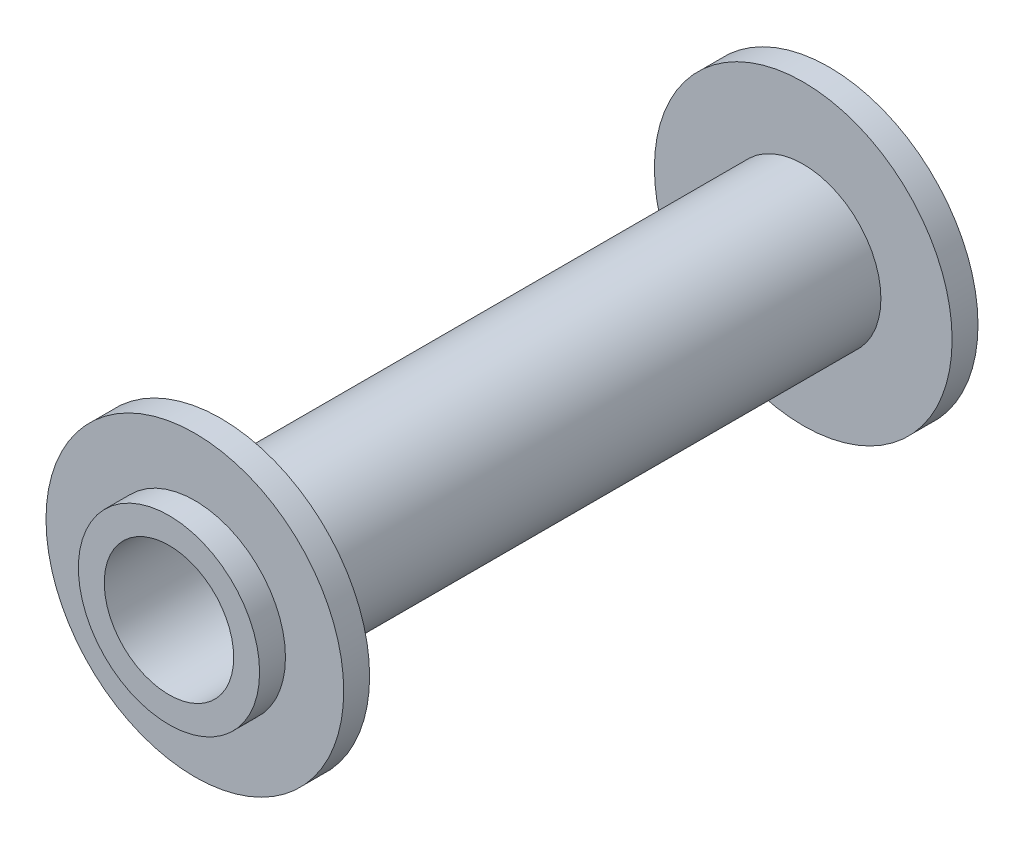
SolidWorks part; units mm, degrees
material "1060 Alloy"
ref_plane "Front Plane" through (0, 0, 0) normal (0, 0, 1) x (1, 0, 0)
ref_plane "Top Plane" through (0, 0, 0) normal (0, 1, 0) x (1, 0, 0)
ref_plane "Right Plane" through (0, 0, 0) normal (1, 0, 0) x (0, 0, -1)
sketch "Sketch2" plane through (0, 0, 0) normal (1, 0, 0) x (0, 0, -1)
  line L0 (0, 0) -> (56.7425, 0) construction
  line L1 (0, 5) -> (0, 7)
  line L2 (4, 6) -> (4, 11.5)
  line L3 (4, 11.5) -> (2, 11.5)
  line L4 (2, 11.5) -> (2, 7)
  line L5 (2, 7) -> (0, 7)
  line L6 (4, 6) -> (49, 6)
  line L7 (49, 6) -> (49, 11.5)
  line L8 (49, 11.5) -> (51, 11.5)
  line L9 (51, 11.5) -> (51, 7)
  line L10 (51, 7) -> (53, 7)
  line L11 (53, 7) -> (53, 5)
  line L12 (53, 5) -> (0, 5)
  dimension "D1" = 11.5
  dimension "D2" = 2
  dimension "D3" = 2
  dimension "D4" = 1
  dimension "D5" = 45
  dimension "D6" = 5
  dimension "D8" = 2
revolve "Revolve1" add sketch "Sketch2" angle 360 about L0
